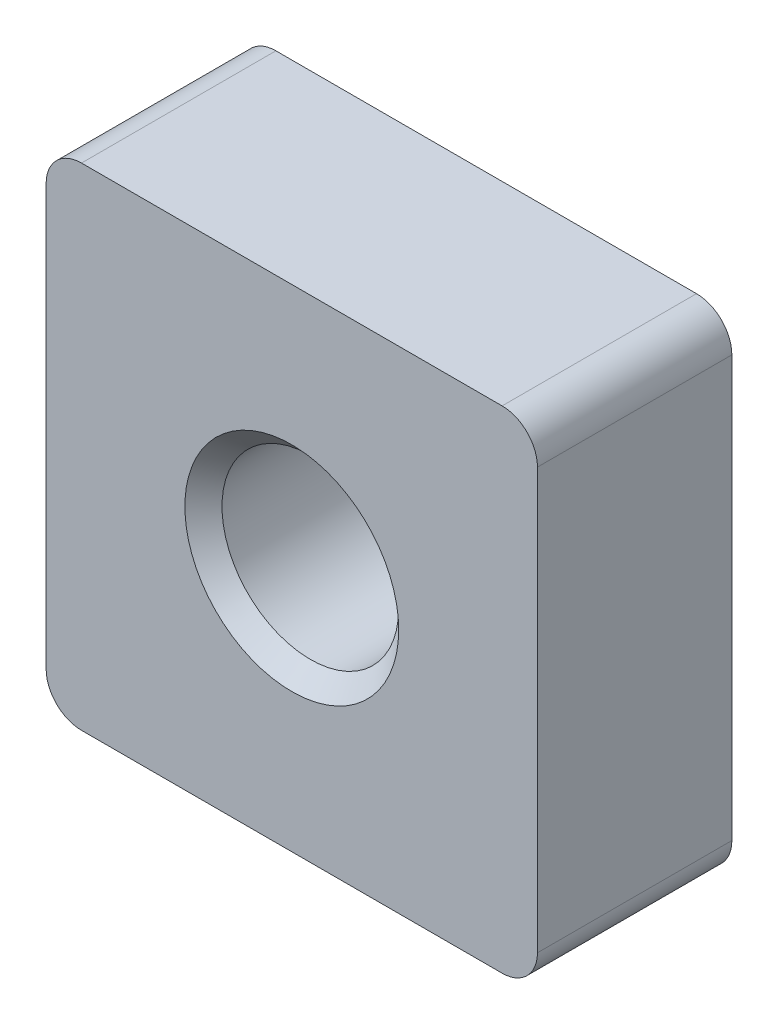
SolidWorks part; units mm, degrees
ref_plane "Спереди" through (0, 0, 0) normal (0, 0, 1) x (1, 0, 0)
ref_plane "Сверху" through (0, 0, 0) normal (0, 1, 0) x (1, 0, 0)
ref_plane "Справа" through (0, 0, 0) normal (1, 0, 0) x (0, 0, -1)
sketch "Эскиз1" plane through (0, 0, 0) normal (0, 0, 1) x (1, 0, 0)
  line L1 (-6.95, -6.95) -> (6.95, -6.95)
  line L2 (-6.95, -6.95) -> (-6.95, 6.95)
  line L3 (-6.95, 6.95) -> (6.95, 6.95)
  line L4 (6.95, -6.95) -> (6.95, 6.95)
  line L5 (-6.95, -6.95) -> (6.95, 6.95) construction
  line L6 (-6.95, 6.95) -> (6.95, -6.95) construction
  point P0 (0, 0)
  dimension "D1" = 13.9
extrude "Бобышка-Вытянуть1" add sketch "Эскиз1" along normal blind 5.5
hole_wizard "Отверстие обработанное метчиком M61" positions "Эскиз2" profile "Эскиз3" tap size "M6" standard "ISO" end condition through all
sketch "Эскиз2" plane through (0, 0, 5.5) normal (0, 0, 1) x (1, 0, 0)
  point P0 (0, 0)
sketch "Эскиз3" plane through (0, 0, 5.5) normal (1, 0, 0) x (0, -1, 0)
  line L0 (0, 0) -> (0, 5.5)
  line L1 (0, 5.5) -> (3.025, 5.5)
  line L2 (2.5, 4.975) -> (2.5, 0.525)
  line L3 (2.5, 0.525) -> (3.025, 0)
  line L5 (3.025, 0) -> (0, 0)
  line L6 (-2.5, 0.525) -> (-3.025, 0) construction
  line L7 (3.025, 5.5) -> (2.5, 4.975)
  line L8 (-3.025, 5.5) -> (-2.5, 4.975) construction
  line L11 (0, -6.35) -> (0, 107.95) construction
  dimension "Диаметр проходного сверла" = 5
  dimension "Глубина проходного сверла" = 5.5
  dimension "Диаметр передней зенковки" = 6.05
  dimension "Угол передней зенковки" = 90
  dimension "Диаметр задней зенковки" = 6.05
  dimension "Угол задней зенковки" = 90
cosmetic thread "Отверстие резьбы1" parameters "D2"=6
fillet "Скругление1" radius 1 4 edges at (6.95, 6.95, 2.75) (-6.95, 6.95, 2.75) (6.95, -6.95, 2.75) (-6.95, -6.95, 2.75)
